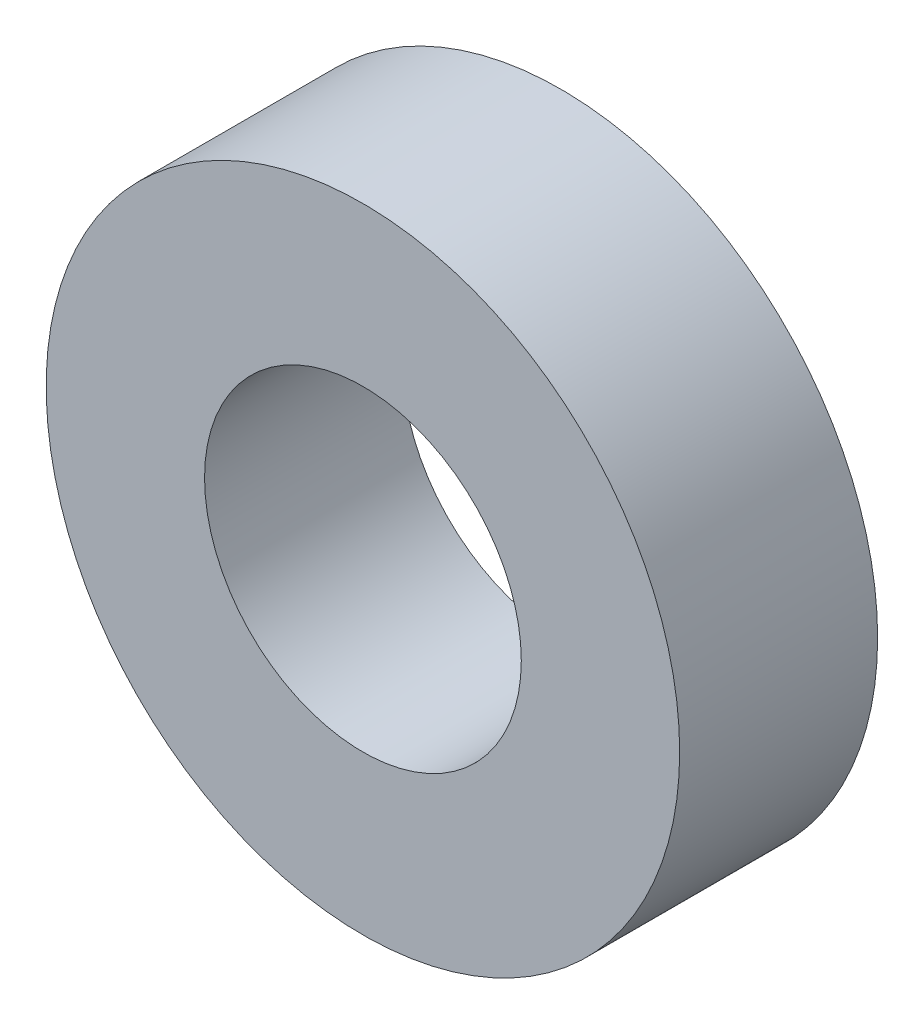
SolidWorks part; units mm, degrees
ref_plane "Plan de face" through (0, 0, 0) normal (0, 0, 1) x (1, 0, 0)
ref_plane "Plan de dessus" through (0, 0, 0) normal (0, 1, 0) x (1, 0, 0)
ref_plane "Plan de droite" through (0, 0, 0) normal (1, 0, 0) x (0, 0, -1)
sketch "Esquisse1" plane through (0, 0, 0) normal (0, 0, 1) x (1, 0, 0)
  circle A0 centre (0, 0) radius 4
  circle A1 centre (0, 0) radius 8
extrude "Extrusion1" add sketch "Esquisse1" along normal blind 5
